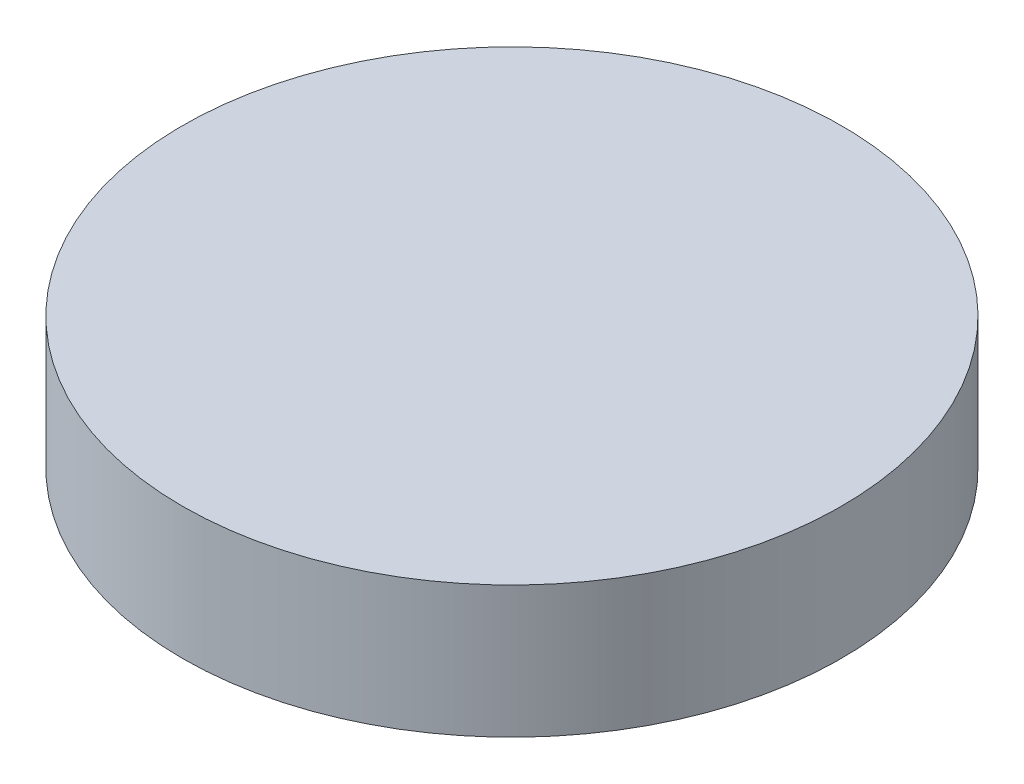
SolidWorks part; units mm, degrees
ref_plane "Front Plane" through (0, 0, 0) normal (0, 0, 1) x (1, 0, 0)
ref_plane "Top Plane" through (0, 0, 0) normal (0, 1, 0) x (1, 0, 0)
ref_plane "Right Plane" through (0, 0, 0) normal (1, 0, 0) x (0, 0, -1)
sketch "Sketch1" plane through (0, 0, 0) normal (0, 1, 0) x (1, 0, 0)
  circle A0 centre (0, 0) radius 5
  dimension "D1" = 10
extrude "Boss-Extrude1" add sketch "Sketch1" along normal blind 2
